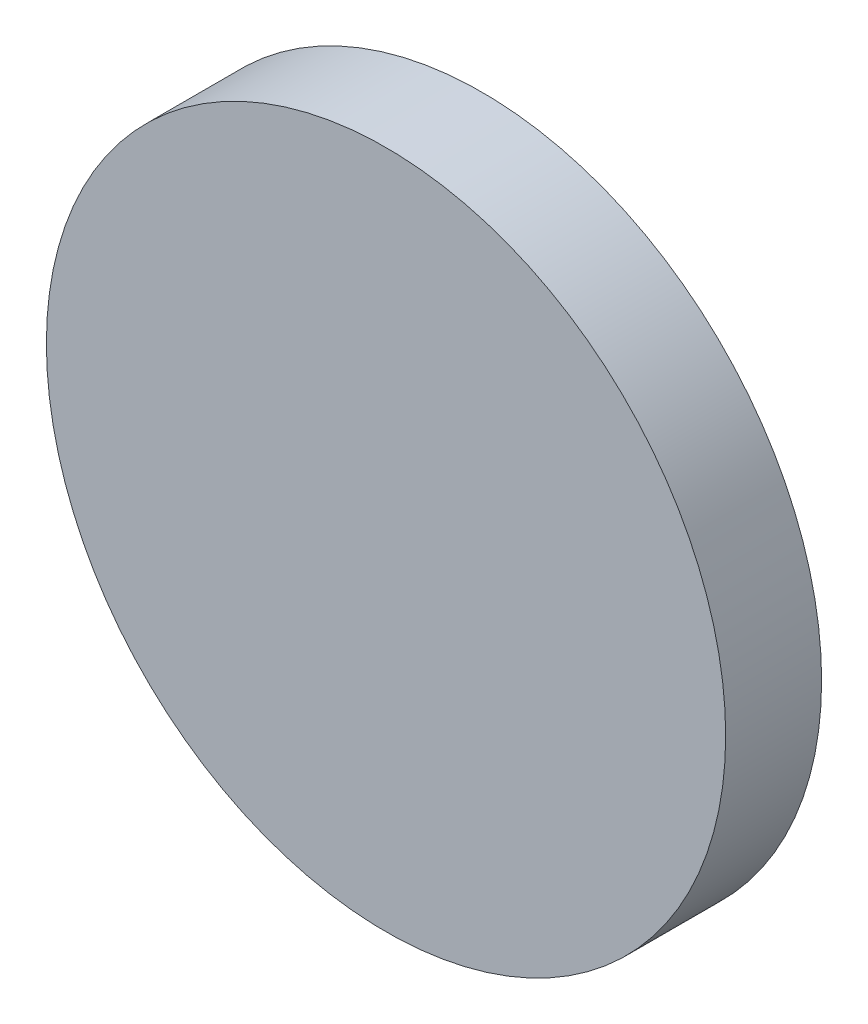
SolidWorks part; units mm, degrees
material "PVC Rígido"
ref_plane "Alzado" through (0, 0, 0) normal (0, 0, 1) x (1, 0, 0)
ref_plane "Planta" through (0, 0, 0) normal (0, 1, 0) x (1, 0, 0)
ref_plane "Vista lateral" through (0, 0, 0) normal (1, 0, 0) x (0, 0, -1)
sketch "Croquis1" plane through (0, 0, 0) normal (0, 0, 1) x (1, 0, 0)
  circle A0 centre (0, 0) radius 3.54
  dimension "D1" = 7.08
extrude "Saliente-Extruir1" add sketch "Croquis1" along normal blind 1
